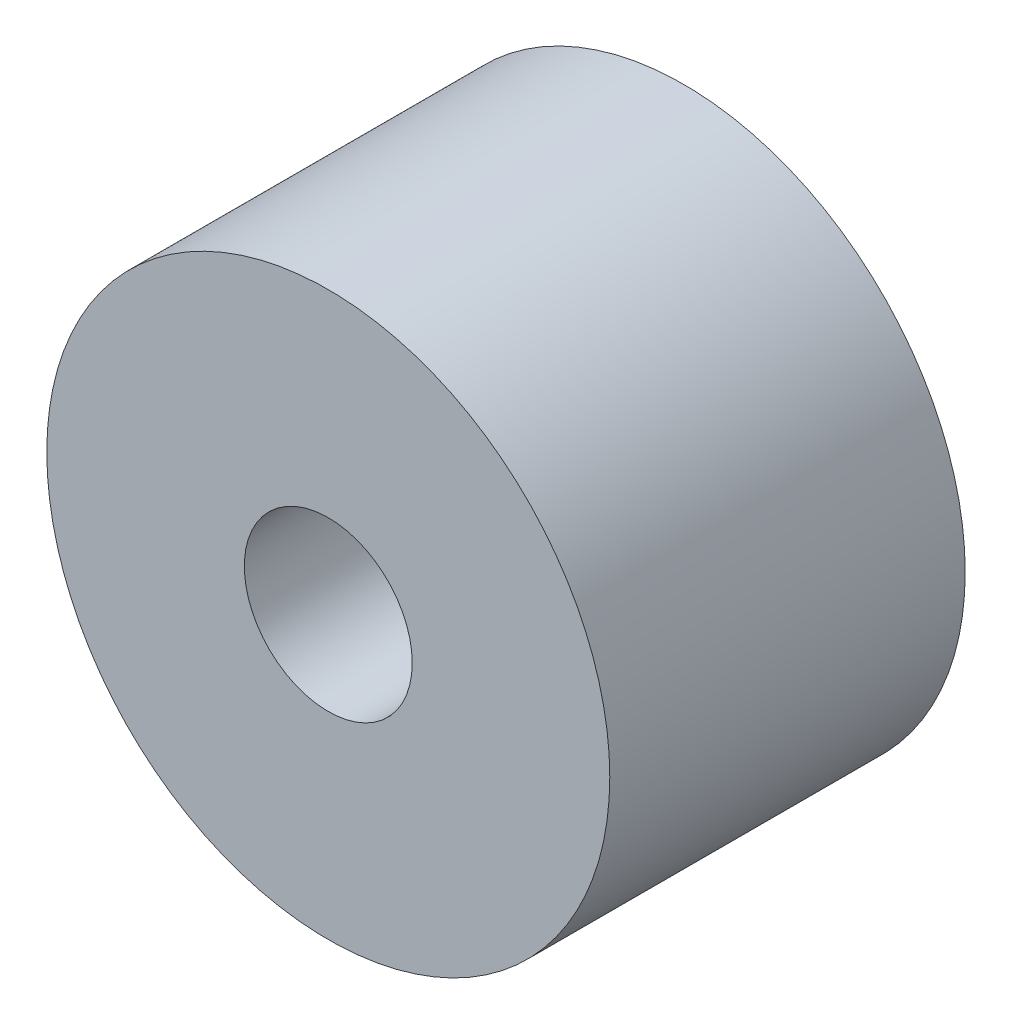
SolidWorks part; units mm, degrees
ref_plane "Front Plane" through (0, 0, 0) normal (0, 0, 1) x (1, 0, 0)
ref_plane "Top Plane" through (0, 0, 0) normal (0, 1, 0) x (1, 0, 0)
ref_plane "Right Plane" through (0, 0, 0) normal (1, 0, 0) x (0, 0, -1)
sketch "Sketch1" plane through (0, 0, 0) normal (0, 0, 1) x (1, 0, 0)
  circle A0 centre (0, 0) radius 10.0584
  circle A1 centre (0, 0) radius 3
  dimension "D1" = 6
  dimension "D2" = 20.1168
extrude "Boss-Extrude1" add sketch "Sketch1" along normal blind 12.7 contours A0
